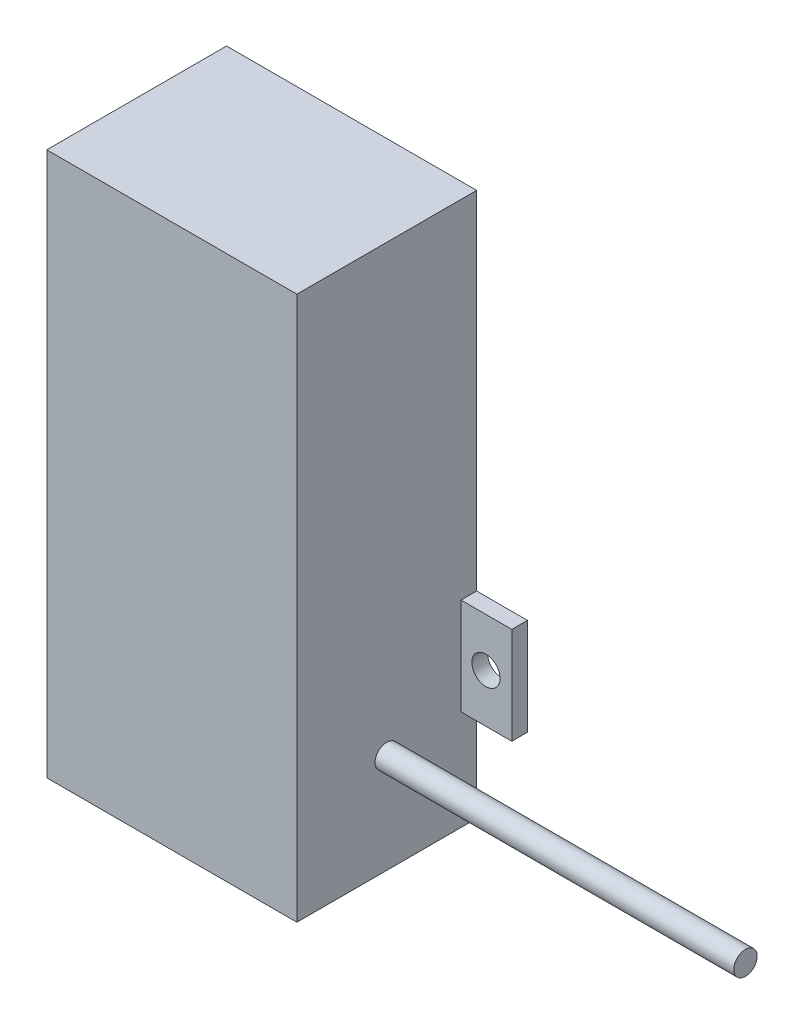
SolidWorks part; units mm, degrees
ref_plane "正面" through (0, 0, 0) normal (0, 0, 1) x (1, 0, 0)
ref_plane "平面" through (0, 0, 0) normal (0, 1, 0) x (1, 0, 0)
ref_plane "右側面" through (0, 0, 0) normal (1, 0, 0) x (0, 0, -1)
sketch "ｽｹｯﾁ1" plane through (0, 0, 0) normal (0, 0, 1) x (1, 0, 0)
  line L1 (34.2791, 29.2729) -> (66.2791, 29.2729)
  line L2 (34.2791, 29.2729) -> (34.2791, -40.3271)
  line L3 (34.2791, -40.3271) -> (66.2791, -40.3271)
  line L4 (66.2791, 29.2729) -> (66.2791, -40.3271)
  dimension "D1" = 69.6
  dimension "D2" = 32
extrude "ﾎﾞｽ - 押し出し1" add sketch "ｽｹｯﾁ1" along normal blind 23
sketch "ｽｹｯﾁ2" plane through (66.2791, 0, 0) normal (1, 0, 0) x (0, 0, -1)
  line L0 (-11.5, -40.3271) -> (-11.5, -27.6271)
  line L1 (-23, -40.3271) -> (0, -40.3271) construction
  circle A0 centre (-11.5, -27.6271) radius 1.5
  dimension "D2" = 3
  dimension "D1" = 12.7
extrude "ﾎﾞｽ - 押し出し2" add sketch "ｽｹｯﾁ2" along normal blind 45.9
sketch "ｽｹｯﾁ3" plane through (66.2791, 0, 0) normal (1, 0, 0) x (0, 0, -1)
  line L0 (0, -40.3271) -> (0, -23.1221)
  line L1 (0, -40.3271) -> (0, 29.2729) construction
  line L3 (0, -23.1221) -> (-2, -23.1221)
  line L4 (0, -23.1221) -> (0, -19.5221)
  line L5 (0, -19.5221) -> (-2, -19.5221)
  line L6 (-2, -23.1221) -> (-2, -19.5221)
  line M5 (0, -40.3271) -> (0, 29.2729)
  dimension "D1" = 17.205
  dimension "D2" = 3.6
  dimension "D3" = 2
extrude "ﾎﾞｽ - 押し出し3" add sketch "ｽｹｯﾁ3" along normal blind 4.5 contours L6 L3 L5 M5
sketch "ｽｹｯﾁ5" plane through (0, 29.2729, 0) normal (0, 1, 0) x (1, 0, 0)
  line L0 (66.2791, -23) -> (34.2791, -23) construction
  line L1 (34.2791, 0) -> (50.2791, 0)
  line L2 (34.2791, 0) -> (34.2791, -23)
  line L3 (34.2791, -23) -> (50.2791, -23)
  line L4 (50.2791, 0) -> (50.2791, -23)
extrude "ｶｯﾄ - 押し出し1" cut sketch "ｽｹｯﾁ5" against normal blind 71.5
sketch "ｽｹｯﾁ6" plane through (0, 0, 2) normal (0, 0, 1) x (1, 0, 0)
  line L0 (70.7791, -23.1221) -> (70.7791, -19.5221) construction
  line L1 (70.7791, -19.5221) -> (66.2791, -19.5221)
  line L2 (70.7791, -19.5221) -> (70.7791, -23.1221)
  line L3 (70.7791, -23.1221) -> (66.2791, -23.1221)
  line L4 (66.2791, -19.5221) -> (66.2791, -23.1221)
  line L5 (70.7791, -19.5221) -> (66.2791, -19.5221) construction
  line L6 (70.7791, -23.1221) -> (66.2791, -23.1221) construction
extrude "ｶｯﾄ - 押し出し2" cut sketch "ｽｹｯﾁ6" against normal blind 1
sketch "ｽｹｯﾁ7" plane through (66.2791, 0, 0) normal (1, 0, 0) x (0, 0, -1)
  line L1 (0, -19.5221) -> (-2, -19.5221)
  line L2 (0, -19.5221) -> (0, -15.1221)
  line L3 (0, -15.1221) -> (-2, -15.1221)
  line L4 (-2, -19.5221) -> (-2, -15.1221)
  dimension "D1" = 4.4
  dimension "D2" = 2
extrude "ﾎﾞｽ - 押し出し4" add sketch "ｽｹｯﾁ7" along normal blind 6.5
sketch "ｽｹｯﾁ9" plane through (70.7791, 0, 0) normal (1, 0, 0) x (0, 0, -1)
  line L0 (-1, -23.1221) -> (-1, -19.5221) construction
  line L1 (-1, -23.1221) -> (0, -23.1221)
  line L2 (-1, -23.1221) -> (-1, -21.3221)
  line L3 (-1, -21.3221) -> (0, -21.3221)
  line L4 (0, -23.1221) -> (0, -21.3221)
  line L5 (0, -23.1221) -> (0, -19.5221) construction
extrude "ｶｯﾄ - 押し出し3" cut sketch "ｽｹｯﾁ9" against normal blind 4.5
mirror "ﾐﾗｰ4" about plane through (66.2791, -21.3221, 1) normal (0, 1, 0) of "ﾎﾞｽ - 押し出し4", "ｶｯﾄ - 押し出し3"
sketch "ｽｹｯﾁ10" plane through (0, -19.5221, 0) normal (0, -1, 0) x (1, 0, 0)
  line L0 (72.7791, 0) -> (66.2791, 0) construction
  line L1 (72.7791, 2) -> (71.2791, 2)
  line L2 (72.7791, 2) -> (72.7791, 0)
  line L3 (72.7791, 0) -> (71.2791, 0)
  line L4 (71.2791, 2) -> (71.2791, 0)
  dimension "D1" = 1.5
extrude "ﾎﾞｽ - 押し出し5" add sketch "ｽｹｯﾁ10" along normal blind 4.5
mirror "ﾐﾗｰ25" about plane through (50.2791, -42.2271, 0) normal (1, 0, 0) of "ﾎﾞｽ - 押し出し4", "ﾎﾞｽ - 押し出し5", "ﾎﾞｽ - 押し出し2", "ﾎﾞｽ - 押し出し1"
sketch "ｽｹｯﾁ12" plane through (27.7791, 0, 0) normal (-1, 0, 0) x (0, 0, 1)
  line L1 (0, -24.0221) -> (2, -24.0221)
  line L2 (0, -24.0221) -> (0, -28.4172)
  line L3 (0, -28.4172) -> (2, -28.4172)
  line L4 (2, -24.0221) -> (2, -28.4172)
extrude "ﾎﾞｽ - 押し出し6" add sketch "ｽｹｯﾁ12" against normal blind 7.5
sketch "ｽｹｯﾁ14" plane through (0, 0, 2) normal (0, 0, 1) x (1, 0, 0)
  line L0 (71.2791, -21.3221) -> (69.4773, -21.3221)
  line L1 (71.2791, -23.1221) -> (71.2791, -19.5221) construction
  circle A0 centre (69.4773, -21.3221) radius 1.8018
sketch "ｽｹｯﾁ15" plane through (66.2791, 0, 0) normal (1, 0, 0) x (0, 0, -1)
  line L1 (-2, -19.5221) -> (0, -19.5221)
  line L2 (-2, -19.5221) -> (-2, -23.1221)
  line L3 (-2, -23.1221) -> (0, -23.1221)
  line L4 (0, -19.5221) -> (0, -23.1221)
extrude "ﾎﾞｽ - 押し出し7" add sketch "ｽｹｯﾁ15" along normal blind 6
extrude "ｶｯﾄ - 押し出し4" cut sketch "ｽｹｯﾁ14" against normal blind 6 contours A0
sketch "ｽｹｯﾁ16" plane through (0, 0, 2) normal (0, 0, 1) x (1, 0, 0)
  line L0 (29.2791, -21.7721) -> (31.0772, -21.7721)
  line L1 (29.2791, -24.0221) -> (29.2791, -19.5221) construction
  circle A0 centre (31.0772, -21.7721) radius 1.7981
sketch "ｽｹｯﾁ17" plane through (34.2791, 0, 0) normal (-1, 0, 0) x (0, 0, 1)
  line L1 (0, -24.0221) -> (2, -24.0221)
  line L2 (0, -24.0221) -> (0, -19.5221)
  line L3 (0, -19.5221) -> (2, -19.5221)
  line L4 (2, -24.0221) -> (2, -19.5221)
extrude "ﾎﾞｽ - 押し出し8" add sketch "ｽｹｯﾁ17" along normal blind 6
extrude "ｶｯﾄ - 押し出し5" cut sketch "ｽｹｯﾁ16" against normal blind 6 contours A0
sketch "ｽｹｯﾁ18" plane through (-11.6209, 0, 0) normal (-1, 0, 0) x (0, 0, 1)
  circle A0 centre (11.5, -27.6271) radius 1.5
extrude "ｶｯﾄ - 押し出し6" cut sketch "ｽｹｯﾁ18" against normal blind 45.9
